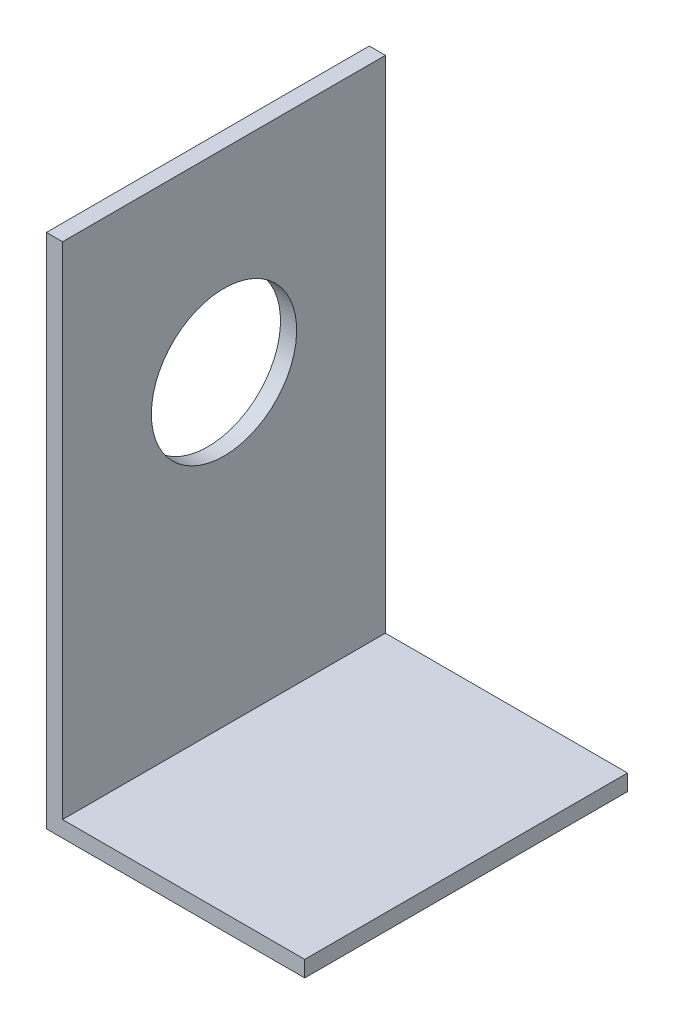
SolidWorks part; units mm, degrees
ref_plane "Front Plane" through (0, 0, 0) normal (0, 0, 1) x (1, 0, 0)
ref_plane "Top Plane" through (0, 0, 0) normal (0, 1, 0) x (1, 0, 0)
ref_plane "Right Plane" through (0, 0, 0) normal (1, 0, 0) x (0, 0, -1)
sketch "Sketch1" plane through (0, 0, 0) normal (0, 0, 1) x (1, 0, 0)
  line L0 (0, 0) -> (0, 101.6)
  line L1 (0, 101.6) -> (3.175, 101.6)
  line L2 (3.175, 101.6) -> (3.175, 3.175)
  line L3 (3.175, 3.175) -> (50.8, 3.175)
  line L4 (50.8, 3.175) -> (50.8, 0)
  line L5 (50.8, 0) -> (0, 0)
  dimension "D1" = 101.6
  dimension "D2" = 50.8
  dimension "D3" = 3.175
  dimension "D4" = 3.175
extrude "Boss-Extrude1" add sketch "Sketch1" along normal blind 63.5
sketch "Sketch2" plane through (0, 0, 0) normal (-1, 0, 0) x (0, 0, 1)
  line L0 (31.75, 101.6) -> (31.75, 0) construction
  line L1 (63.5, 101.6) -> (0, 101.6) construction
  line L2 (63.5, 0) -> (0, 0) construction
  circle A0 centre (31.75, 63.5) radius 14.2875
  dimension "D1" = 28.575
  dimension "D2" = 63.5
extrude "Cut-Extrude1" cut sketch "Sketch2" against normal through all
